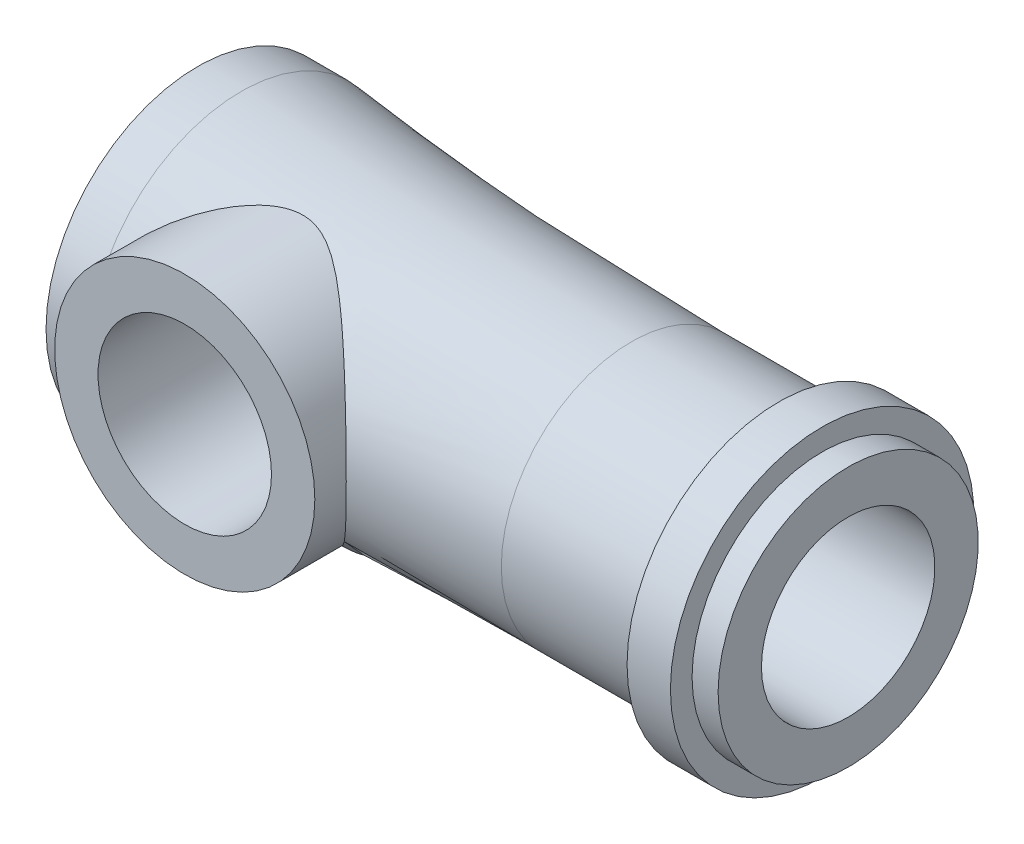
SolidWorks part; units mm, degrees
ref_plane "정면" through (0, 0, 0) normal (0, 0, 1) x (1, 0, 0)
ref_plane "윗면" through (0, 0, 0) normal (0, 1, 0) x (1, 0, 0)
ref_plane "우측면" through (0, 0, 0) normal (1, 0, 0) x (0, 0, -1)
sketch "스케치1" plane through (0, 0, 0) normal (0, 0, 1) x (1, 0, 0)
  line L0 (0, 0) -> (0, 17.5)
  line L1 (0, 17.5) -> (5, 17.5)
  line L2 (0, 0) -> (60, 0) construction
  line L3 (60, 0) -> (60, 10)
  line L4 (60, 10) -> (75, 10)
  line L5 (75, 10) -> (75, 15)
  line L6 (75, 15) -> (72, 15)
  line L7 (72, 15) -> (72, 17.5)
  line L8 (72, 17.5) -> (67, 17.5)
  line L9 (67, 17.5) -> (67, 15)
  line L10 (67, 15) -> (50, 15)
  line L11 (0, 0) -> (60, 0)
  arc A0 (5, 17.5) -> (50, 15) centre (50, 421.25) ccw
  point P14 (0, 0)
  point P15 (0, 0)
  point P16 (0, 0)
  dimension "D1" = 2.5
  dimension "D2" = 3
  dimension "D3" = 5
  dimension "D4" = 15
  dimension "D5" = 5
  dimension "D6" = 50
  dimension "D7" = 75
  dimension "D8" = 20
  dimension "D9" = 30
  dimension "D10" = 35
revolve "회전1" add sketch "스케치1" angle 360 about L2
sketch "스케치2" plane through (0, 0, 0) normal (0, 0, 1) x (1, 0, 0)
  line L1 (0, 17.5) -> (0, -17.5) construction
  circle A0 centre (17.5, 0) radius 15
  point P2 (39.8089, 0)
  point P4 (25.3397, 0)
  dimension "D1" = 30
  dimension "D2" = 2.5
extrude "보스-돌출1" add sketch "스케치2" along normal blind 19
sketch "스케치3" plane through (0, 0, 19) normal (0, 0, 1) x (1, 0, 0)
  circle A4 centre (17.5, 0) radius 10
  circle A5 centre (17.5, 0) radius 15 construction
  dimension "D1" = 20
extrude "컷-돌출1" cut sketch "스케치3" against normal blind 25 contours A4
